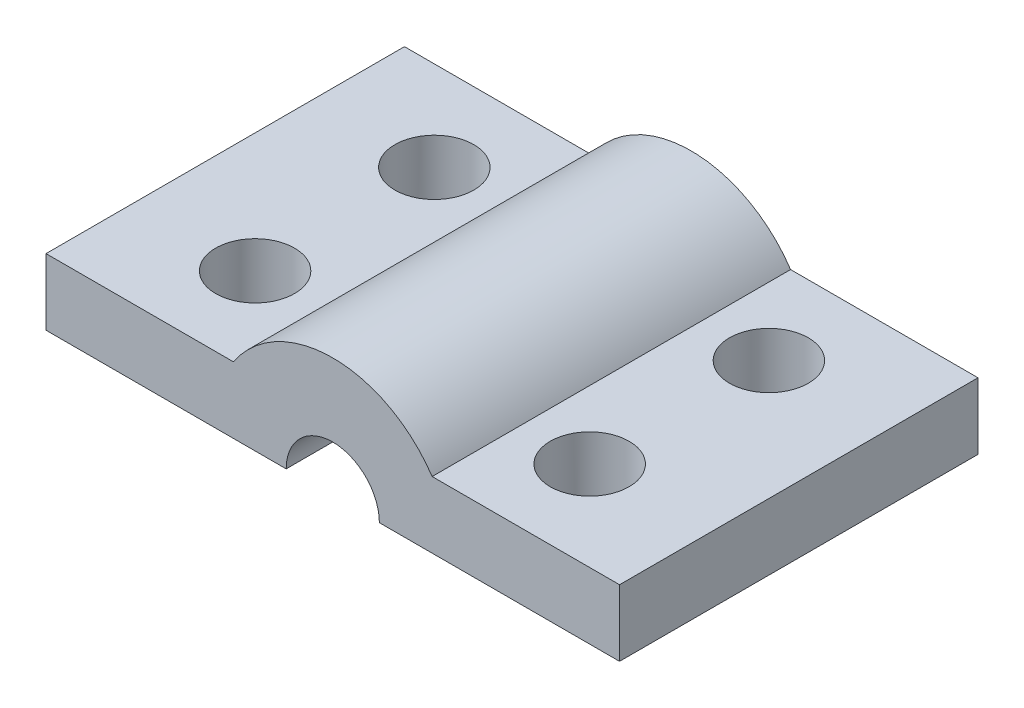
SolidWorks part; units mm, degrees
ref_plane "Front Plane" through (0, 0, 0) normal (0, 0, 1) x (1, 0, 0)
ref_plane "Top Plane" through (0, 0, 0) normal (0, 1, 0) x (1, 0, 0)
ref_plane "Right Plane" through (0, 0, 0) normal (1, 0, 0) x (0, 0, -1)
sketch "Sketch1" plane through (0, 0, 0) normal (0, 0, 1) x (1, 0, 0)
  line L0 (-5, 0) -> (-12, 0)
  line L1 (-12, 0) -> (-12, 2.7775)
  line L2 (-12, 2.7775) -> (-4.1576, 2.7775)
  line L3 (-5, 0) -> (-1.95, 0)
  line L4 (0, 0) -> (0, 5) construction
  line L5 (5, 0) -> (1.95, 0)
  line L6 (12, 2.7775) -> (4.1576, 2.7775)
  line L7 (12, 0) -> (12, 2.7775)
  line L8 (5, 0) -> (12, 0)
  circle A0 centre (0, 0) radius 5
  circle A1 centre (0, 0) radius 1.95
  dimension "D3" = 3.9
  dimension "D4" = 10
  dimension "D1" = 7
  dimension "D2" = 2.7775
extrude "Boss-Extrude1" add sketch "Sketch1" along normal blind 7.5 contours A0 L2 L1 L0 | A1 L4 A0 L3 | L4 A1 L5 A0 | A0 L8 L7 L6
sketch "Sketch2" plane through (0, 2.7775, 0) normal (0, 1, 0) x (1, 0, 0)
  line L0 (-12, -7.5) -> (-12, 0) construction
  circle A0 centre (-7, -3.75) radius 1.65
  point P5 (-12, -3.75)
  dimension "D1" = 3.3
  dimension "D2" = 7
extrude "Cut-Extrude1" cut sketch "Sketch2" against normal through all both and the other way through all
mirror "Mirror1" about plane through (0, 0, 0) normal (1, 0, 0) of "Cut-Extrude1"
mirror "Mirror2" about plane through (0, 0, 0) normal (0, 0, 1) of "Mirror1", "Cut-Extrude1", "Boss-Extrude1"
